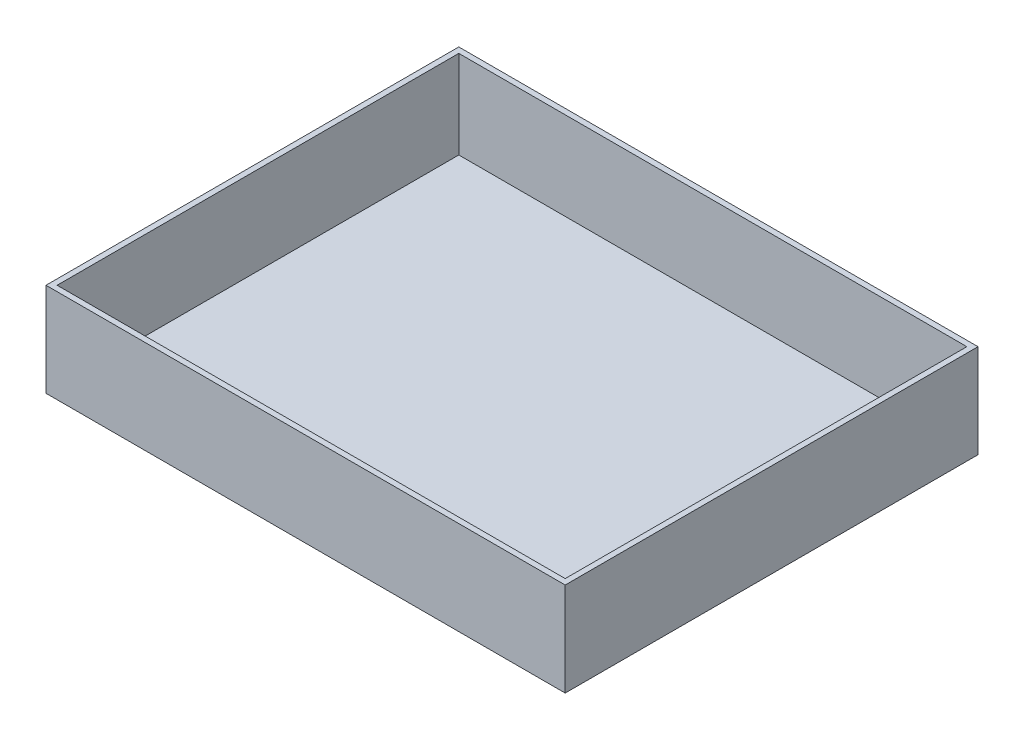
SolidWorks part; units mm, degrees
ref_plane "Front Plane" through (0, 0, 0) normal (0, 0, 1) x (1, 0, 0)
ref_plane "Top Plane" through (0, 0, 0) normal (0, 1, 0) x (1, 0, 0)
ref_plane "Right Plane" through (0, 0, 0) normal (1, 0, 0) x (0, 0, -1)
sketch "Sketch1" plane through (0, 0, 0) normal (0, 1, 0) x (1, 0, 0)
  line L1 (0, 0) -> (466, 0)
  line L2 (0, 0) -> (0, 370.5)
  line L3 (0, 370.5) -> (466, 370.5)
  line L4 (466, 0) -> (466, 370.5)
  dimension "D1" = 370.5
  dimension "D2" = 466
extrude "Boss-Extrude1" add sketch "Sketch1" along normal blind 84 contours L3 L4 L1 L2
sketch "Sketch2" plane through (0, 84, 0) normal (0, 1, 0) x (1, 0, 0)
  line L0 (0, 370.5) -> (466, 370.5) construction
  line L1 (5, 5) -> (461, 5)
  line L2 (5, 5) -> (5, 365.5)
  line L3 (5, 365.5) -> (461, 365.5)
  line L4 (461, 5) -> (461, 365.5)
  line L5 (0, 0) -> (0, 370.5) construction
  line L6 (0, 0) -> (466, 0) construction
  line L7 (466, 0) -> (466, 370.5) construction
  dimension "D1" = 5
  dimension "D2" = 5
  dimension "D3" = 5
  dimension "D4" = 5
extrude "Cut-Extrude1" cut sketch "Sketch2" against normal blind 79
